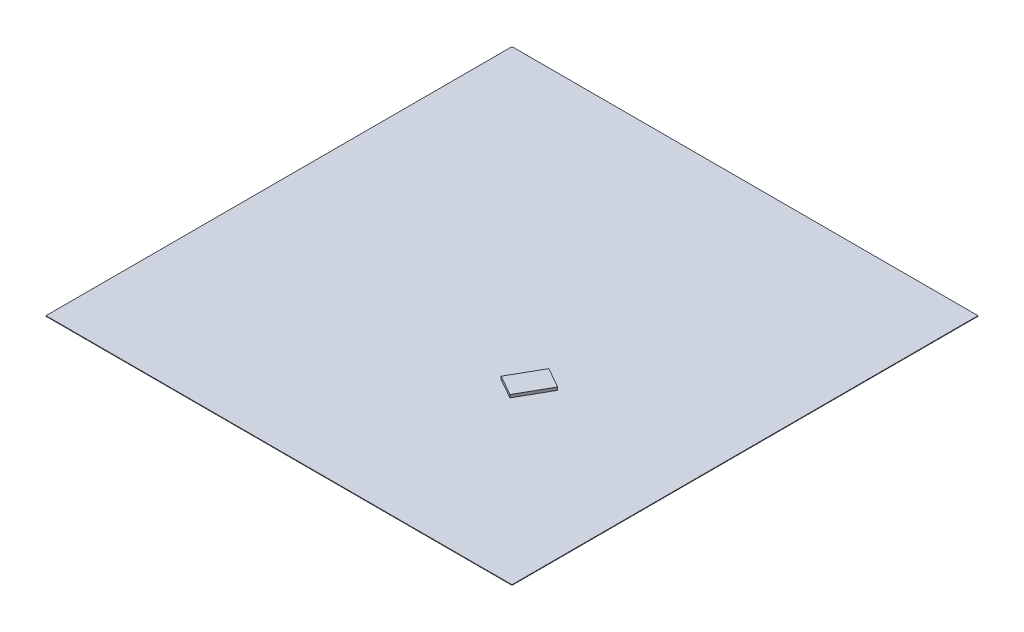
SolidWorks part; units mm, degrees
ref_plane "Front Plane" through (0, 0, 0) normal (0, 0, 1) x (1, 0, 0)
ref_plane "Top Plane" through (0, 0, 0) normal (0, 1, 0) x (1, 0, 0)
ref_plane "Right Plane" through (0, 0, 0) normal (1, 0, 0) x (0, 0, -1)
sketch "Sketch1" plane through (0, 0, 0) normal (0, 1, 0) x (1, 0, 0)
  line L1 (-43023.622, 47496.063) -> (36976.378, 47496.063)
  line L2 (-43023.622, 47496.063) -> (-43023.622, -32503.937)
  line L3 (-43023.622, -32503.937) -> (36976.378, -32503.937)
  line L4 (36976.378, 47496.063) -> (36976.378, -32503.937)
  dimension "D1" = 80000
  dimension "D2" = 80000
extrude "Boss-Extrude1" add sketch "Sketch1" along normal mid plane 100
sketch "Sketch2" plane through (0, 50, 0) normal (0, 1, 0) x (1, 0, 0)
  line L0 (5550.1659, -2934.3363) -> (9030.2547, -4906.3866)
  line L1 (5550.1659, -2934.3363) -> (8508.2414, 2285.7969)
  line L2 (9030.2547, -4906.3866) -> (11988.3301, 313.7466)
  line L3 (8508.2414, 2285.7969) -> (11988.3301, 313.7466)
  dimension "D1" = 6000
  dimension "D2" = 4000
extrude "Boss-Extrude2" add sketch "Sketch2" along normal blind 500
